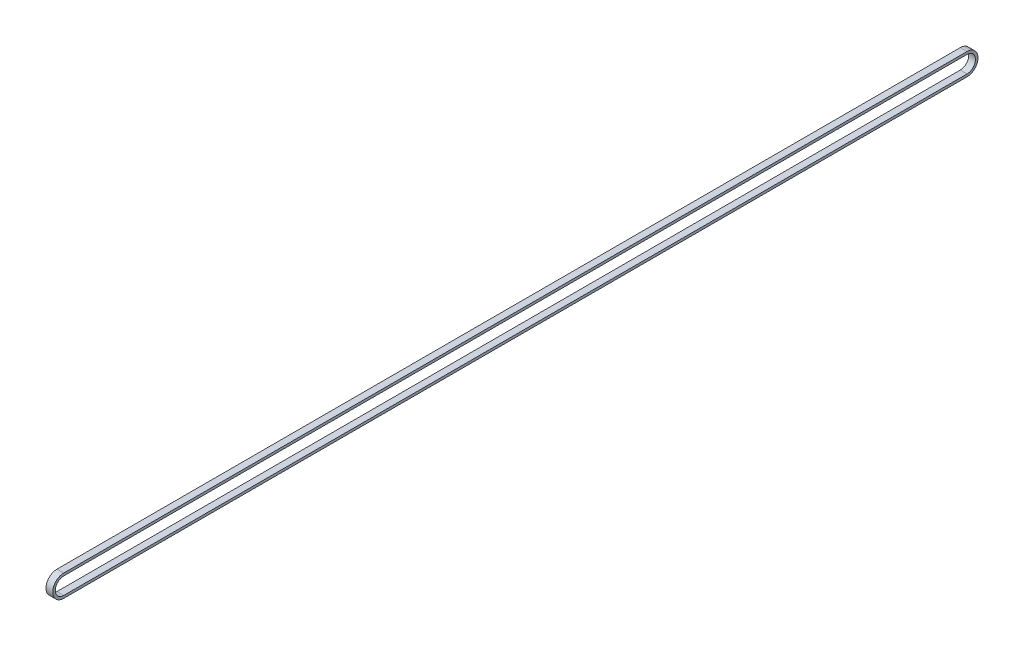
SolidWorks part; units mm, degrees
ref_plane "前视基准面" through (0, 0, 0) normal (0, 0, 1) x (1, 0, 0)
ref_plane "上视基准面" through (0, 0, 0) normal (0, 1, 0) x (1, 0, 0)
ref_plane "右视基准面" through (0, 0, 0) normal (1, 0, 0) x (0, 0, -1)
other "Configuration Table"
sketch "草图1" plane through (0, 0, 0) normal (1, 0, 0) x (0, 0, -1)
  line L0 (0, 0) -> (1070, 0)
  line L1 (0, 20) -> (1070, 20)
  line L2 (0, 23) -> (1070, 23)
  line L3 (0, -3) -> (1070, -3)
  arc A0 (0, 0) -> (0, 20) centre (0, 10) cw
  arc A1 (1070, 20) -> (1070, 0) centre (1070, 10) cw
  arc A2 (1070, 23) -> (1070, -3) centre (1070, 10) cw
  arc A3 (0, -3) -> (0, 23) centre (0, 10) cw
  dimension "D2" = 10
  dimension "D3" = 10
  dimension "D1" = 1070
  dimension "D4" = 3
extrude "凸台-拉伸1" add sketch "草图1" along normal blind 8
